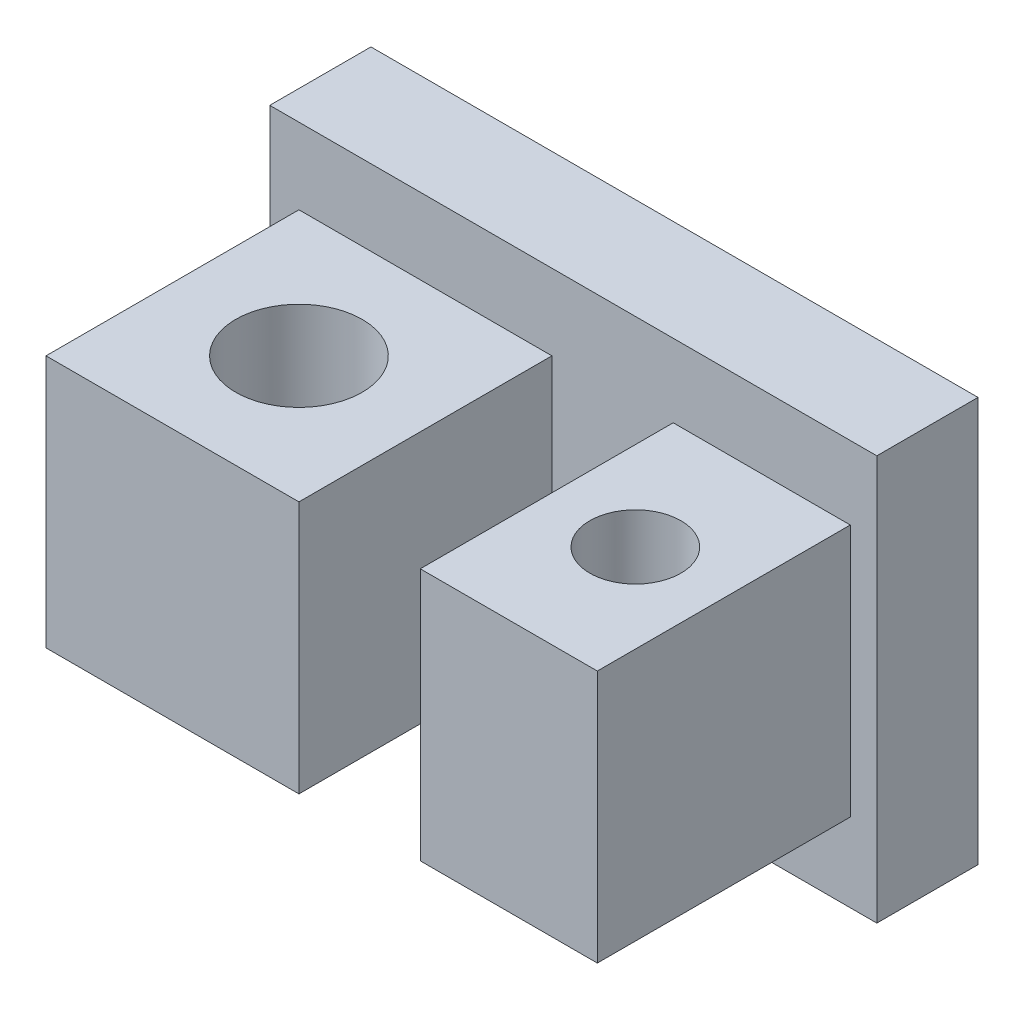
SolidWorks part; units mm, degrees
ref_plane "前基準面" through (0, 0, 0) normal (0, 0, 1) x (1, 0, 0)
ref_plane "上基準面" through (0, 0, 0) normal (0, 1, 0) x (1, 0, 0)
ref_plane "右基準面" through (0, 0, 0) normal (1, 0, 0) x (0, 0, -1)
sketch "草圖1" plane through (0, 0, 0) normal (0, 0, 1) x (1, 0, 0)
  line L1 (-4.5418, 4.026) -> (7.4582, 4.026)
  line L2 (-4.5418, 4.026) -> (-4.5418, -3.974)
  line L3 (-4.5418, -3.974) -> (7.4582, -3.974)
  line L4 (7.4582, 4.026) -> (7.4582, -3.974)
  dimension "D1" = 12
  dimension "D2" = 8
extrude "填料-伸長1" add sketch "草圖1" along normal blind 2
sketch "草圖3" plane through (0, 0, 0) normal (0, 0, 1) x (1, 0, 0)
  line L0 (-4.5418, 0.026) -> (7.4582, 0.026) construction
  line L1 (-3.965, 2.526) -> (1.035, 2.526)
  line L2 (-3.965, 2.526) -> (-3.965, -2.474)
  line L3 (-3.965, -2.474) -> (1.035, -2.474)
  line L4 (1.035, 2.526) -> (1.035, -2.474)
  line L5 (-4.5418, 4.026) -> (-4.5418, -3.974) construction
  line L6 (7.4582, -3.974) -> (7.4582, 4.026) construction
  line L7 (1.4582, 4.026) -> (1.4582, -3.974) construction
  line L8 (7.4582, 4.026) -> (-4.5418, 4.026) construction
  line L9 (-4.5418, -3.974) -> (7.4582, -3.974) construction
  dimension "D1" = 5
  dimension "D2" = 5
extrude "填料-伸長2" add sketch "草圖3" along normal blind 7
sketch "草圖5" plane through (0, 0, 0) normal (0, 1, 0) x (1, 0, 0)
  line L0 (-3.965, -4.5) -> (1.035, -4.5) construction
  line L1 (-3.965, -7) -> (-3.965, -2) construction
  line L2 (1.035, -7) -> (1.035, -2) construction
  line L3 (-1.465, -7) -> (-1.465, -2) construction
  line L4 (-3.965, -7) -> (1.035, -7) construction
  line L5 (1.035, -2) -> (-3.965, -2) construction
  circle A0 centre (-1.465, -4.5) radius 1.25
  dimension "D1" = 2.5
extrude "除料-伸長2" cut sketch "草圖5" against normal blind 5 and the other way blind 5
sketch "草圖6" plane through (0, 0, 0) normal (0, 0, 1) x (1, 0, 0)
  line L6 (3.4331, 2.5792) -> (6.9331, 2.5792)
  line L7 (3.4331, 2.5792) -> (3.4331, -2.4208)
  line L8 (3.4331, -2.4208) -> (6.9331, -2.4208)
  line L9 (6.9331, 2.5792) -> (6.9331, -2.4208)
  dimension "D1" = 5
  dimension "D2" = 3.5
extrude "填料-伸長3" add sketch "草圖6" along normal blind 7
sketch "草圖8" plane through (0, 0, 0) normal (0, 1, 0) x (1, 0, 0)
  circle A0 centre (5.185, -4.5) radius 0.9
  circle A3 centre (-1.465, -4.5) radius 1.25 construction
  dimension "D1" = 1.8
  dimension "D2" = 4.5
extrude "除料-伸長3" cut sketch "草圖8" against normal blind 7 and the other way blind 7
